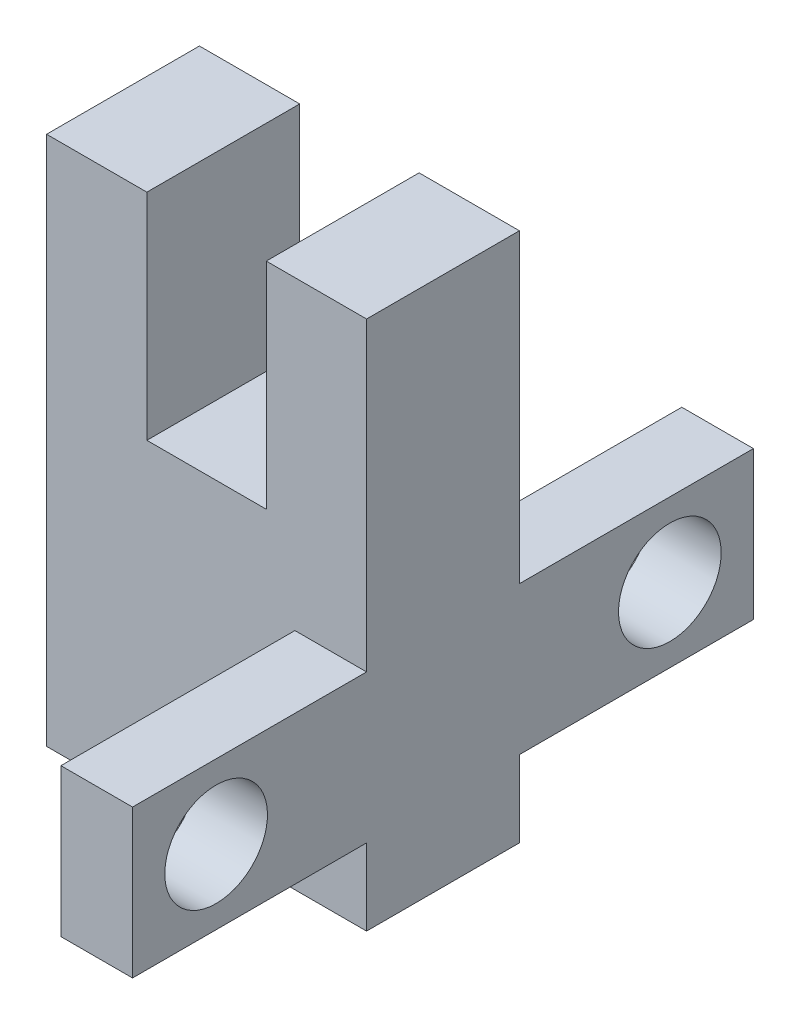
SolidWorks part; units mm, degrees
ref_plane "前视基准面" through (0, 0, 0) normal (0, 0, 1) x (1, 0, 0)
ref_plane "上视基准面" through (0, 0, 0) normal (0, 1, 0) x (1, 0, 0)
ref_plane "右视基准面" through (0, 0, 0) normal (1, 0, 0) x (0, 0, -1)
sketch "草图1" plane through (0, 0, 0) normal (0, 0, 1) x (1, 0, 0)
  line L1 (0, 0) -> (13.4, 0)
  line L2 (0, 0) -> (0, 22.2)
  line L3 (0, 22.2) -> (13.4, 22.2)
  line L4 (13.4, 0) -> (13.4, 22.2)
  dimension "D1" = 22.2
  dimension "D2" = 13.4
extrude "凸台-拉伸1" add sketch "草图1" along normal blind 6.4
sketch "草图2" plane through (0, 0, 6.4) normal (0, 0, 1) x (1, 0, 0)
  line L0 (6.7, 22.2) -> (6.7, 5.9556) construction
  line L1 (13.4, 22.2) -> (0, 22.2) construction
  line L3 (4.2, 22.2) -> (9.2, 22.2)
  line L4 (4.2, 22.2) -> (4.2, 13.2)
  line L5 (4.2, 13.2) -> (9.2, 13.2)
  line L6 (9.2, 22.2) -> (9.2, 13.2)
  dimension "D1" = 9
  dimension "D2" = 5
extrude "切除-拉伸1" cut sketch "草图2" against normal blind 6.4
sketch "草图3" plane through (0, 0, 6.4) normal (0, 0, 1) x (1, 0, 0)
  line L0 (13.4, 0) -> (13.4, 22.2) construction
  line L1 (13.4, 9.4) -> (10.4, 9.4)
  line L2 (13.4, 9.4) -> (13.4, 3.2)
  line L3 (13.4, 3.2) -> (10.4, 3.2)
  line L4 (10.4, 9.4) -> (10.4, 3.2)
  line L5 (13.4, 6.3) -> (7.0333, 6.3) construction
  line L6 (0, 0) -> (13.4, 0) construction
  dimension "D1" = 3
  dimension "D2" = 6.2
  dimension "D3" = 6.3
extrude "凸台-拉伸2" add sketch "草图3" along normal blind 9.8
ref_plane "基准面1" through (0, 0, 3.2) normal (0, 0, -1) x (-1, 0, 0)
mirror "镜向1" about plane through (0, 0, 3.2) normal (0, 0, -1) of "凸台-拉伸2"
sketch "草图4" plane through (10.4, 0, 0) normal (-1, 0, 0) x (0, 0, 1)
  line L0 (3.2, 0) -> (3.2, 20.2048) construction
  line L1 (6.4, 0) -> (0, 0) construction
  line L2 (3.2, 7.37) -> (3.2, -7.37) construction
  line L3 (-9.8, 6.3) -> (16.2, 6.3) construction
  line L4 (-9.8, 9.4) -> (-9.8, 3.2) construction
  line L5 (16.2, 9.4) -> (16.2, 3.2) construction
  circle A0 centre (-6.3, 6.3) radius 2.15
  circle A1 centre (12.7, 6.3) radius 2.15
  point P14 (0, 0)
  point P15 (0, 0)
  point P16 (0, 0)
  dimension "D1" = 4.3
  dimension "D2" = 19
extrude "切除-拉伸2" cut sketch "草图4" against normal blind 9.8
